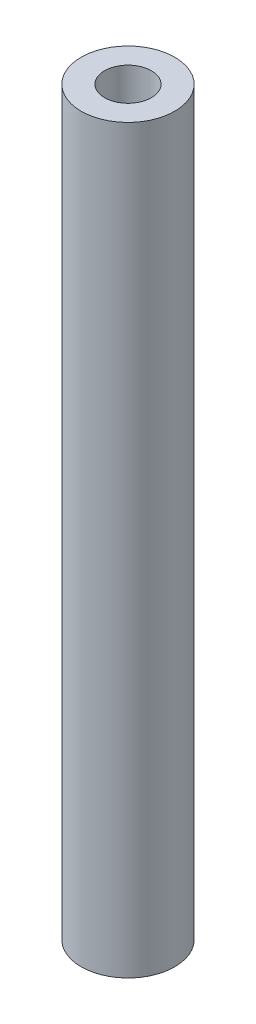
SolidWorks part; units mm, degrees
ref_plane "Front Plane" through (0, 0, 0) normal (0, 0, 1) x (1, 0, 0)
ref_plane "Top Plane" through (0, 0, 0) normal (0, 1, 0) x (1, 0, 0)
ref_plane "Right Plane" through (0, 0, 0) normal (1, 0, 0) x (0, 0, -1)
sketch "Sketch1" plane through (0, 0, 0) normal (0, 1, 0) x (1, 0, 0)
  circle A0 centre (0, 0) radius 3
  circle A1 centre (0, 0) radius 6
  dimension "D1" = 6
  dimension "D2" = 12
extrude "Boss-Extrude1" add sketch "Sketch1" along normal blind 95
